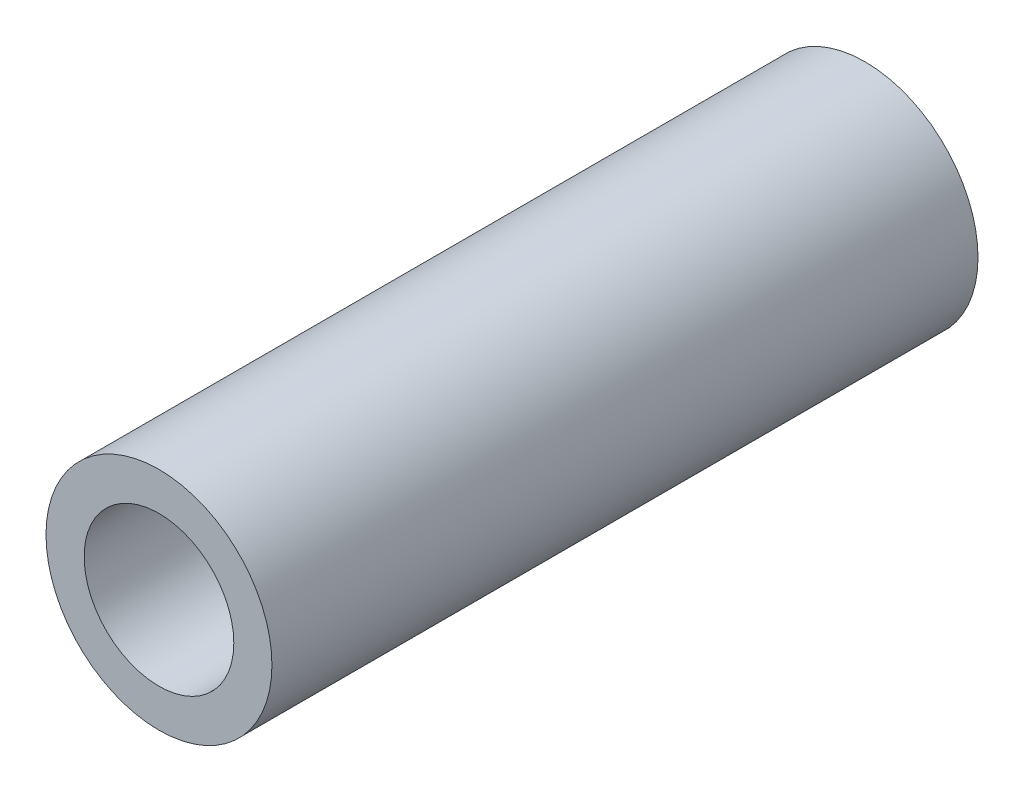
SolidWorks part; units mm, degrees
ref_plane "Front Plane" through (0, 0, 0) normal (0, 0, 1) x (1, 0, 0)
ref_plane "Top Plane" through (0, 0, 0) normal (0, 1, 0) x (1, 0, 0)
ref_plane "Right Plane" through (0, 0, 0) normal (1, 0, 0) x (0, 0, -1)
sketch "Sketch1" plane through (0, 0, 0) normal (0, 0, 1) x (1, 0, 0)
  circle A0 centre (0, 0) radius 4
  circle A1 centre (0, 0) radius 2.65
  dimension "OD" = 8
  dimension "ID" = 5.3
extrude "Extrude1" add sketch "Sketch1" along normal mid plane 25
sketch "Sketch2" plane through (0, 0, 0) normal (1, 0, 0) x (0, 0, -1)
  line L0 (-12.5, -2.65) -> (12.5, -2.65) construction
  line L3 (12.5, 2.65) -> (-12.5, 2.65) construction
  line L5 (-12.5, -2.65) -> (12.5, -2.65)
  line L6 (12.5, 2.65) -> (-12.5, 2.65)
sketch "Sketch4" plane through (0, 0, 12.5) normal (0, 0, 1) x (1, 0, 0)
  line L0 (0, 0) -> (-1.8738, 1.8738)
  line L1 (0, -4.4) -> (0, 4.4) construction
  circle A0 centre (0, 0) radius 2.65 construction
  dimension "D1" = 45
